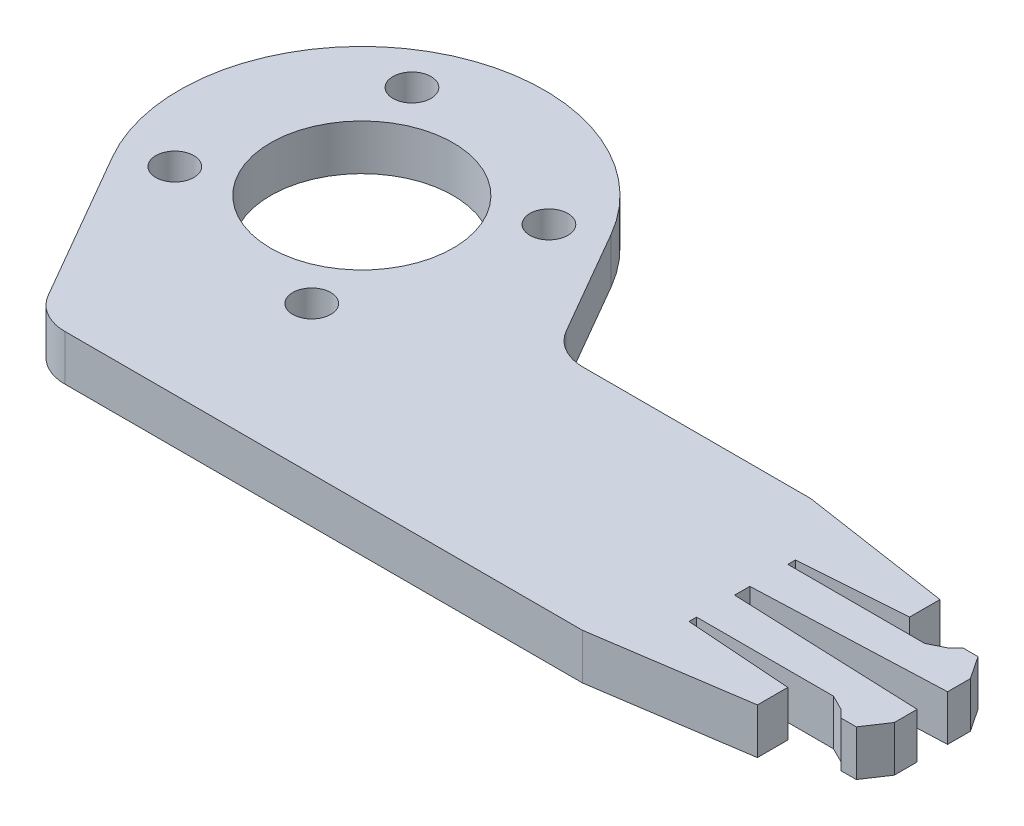
SolidWorks part; units mm, degrees
material "Lasercut ABS"
ref_plane "Front Plane" through (0, 0, 0) normal (0, 0, 1) x (1, 0, 0)
ref_plane "Top Plane" through (0, 0, 0) normal (0, 1, 0) x (1, 0, 0)
ref_plane "Right Plane" through (0, 0, 0) normal (1, 0, 0) x (0, 0, -1)
sketch "Sketch1" plane through (0, 0, 0) normal (0, 1, 0) x (1, 0, 0)
  line L0 (0, 0) -> (0, -10) construction
  line L1 (-4.5, 7.7942) -> (4.5, -7.7942) construction
  line L2 (-7.7942, -4.5) -> (7.7942, 4.5) construction
  line L3 (10.3923, 6) -> (15.2998, -2.5)
  line L4 (15.2998, -2.5) -> (32, -2.5)
  line L5 (-10.3923, -6) -> (-3.7528, -17.5)
  line L6 (-3.7528, -17.5) -> (32, -17.5)
  circle A0 centre (0, 0) radius 6
  circle A1 centre (0, 0) radius 9 construction
  circle A2 centre (7.7942, 4.5) radius 1.25
  circle A3 centre (-4.5, 7.7942) radius 1.25
  circle A4 centre (-7.7942, -4.5) radius 1.25
  circle A5 centre (4.5, -7.7942) radius 1.25
  arc A6 (10.3923, 6) -> (-10.3923, -6) centre (0, 0) ccw
  line B0 (32, -10) -> (35, -10) construction
  line B1 (35, -9.5) -> (35, -10.5)
  line B2 (35, -9.5) -> (47.5, -9)
  line B3 (47.5, -9) -> (47.5, -7.5)
  line B4 (47.5, -7.5) -> (46.5, -6)
  line B5 (46.5, -6) -> (45.5, -6)
  line B6 (45.5, -6) -> (45, -6.5)
  line B7 (45, -6.5) -> (44, -7)
  line B8 (44, -7) -> (35, -7)
  line B9 (35, -7) -> (35, -6.5)
  line B10 (35, -6.5) -> (42, -6)
  line B11 (42, -6) -> (42, -4)
  line B12 (42, -4) -> (32, -2.5)
  line B13 (35, -10.5) -> (47.5, -11)
  line B14 (47.5, -11) -> (47.5, -12.5)
  line B15 (47.5, -12.5) -> (46.5, -14)
  line B16 (46.5, -14) -> (45.5, -14)
  line B17 (45.5, -14) -> (45, -13.5)
  line B18 (45, -13.5) -> (44, -13)
  line B19 (44, -13) -> (35, -13)
  line B20 (35, -13) -> (35, -13.5)
  line B21 (35, -13.5) -> (42, -14)
  line B22 (42, -14) -> (42, -16)
  line B23 (42, -16) -> (32, -17.5)
  dimension "D1" = 12
  dimension "D5" = 18
  dimension "D6" = 2.5
  dimension "D7" = 24
  dimension "D2" = 10
  dimension "D3" = 42
  dimension "D4" = 30
sketch_block_instance "Block-Snap-Textile-1"
sketch_block "Block-Snap-Textile" parameters "D1"=3, "D2"=1, "D3"=2, "D4"=1.5, "D5"=10, "D6"=0.5, "D7"=9, "D8"=1, "D9"=0.5, "D10"=0.5, "D11"=0.5, "D12"=1, "D13"=12.5, "D14"=0.5, "D15"=0.5, "D16"=1.5, "D17"=1.5
extrude "Boss-Extrude1" add sketch "Sketch1" along normal mid plane 3 contours B23 B22 B21 B20 B19 B18 B17 B16 B15 B14 B13 B1 B2 B3 B4 B5 B6 B7 B8 B9 B10 B11 B12 L4 L3 A6 L5 L6 A5 A4 A3 A2 A0
fillet "Fillet1" radius 3 2 edges at (15.2998, 0, 2.5) (-3.7528, 0, 17.5)
sketch "Sketch2" plane through (0, 1.5, 0) normal (0, -1, 0) x (1, 0, 0)
  line L0 (28, 9) -> (12, 9) construction
  line L1 (28, 12.5) -> (12, 12.5) construction
  text T0 "M8" font "1CamBam_Stick_3" height 2.5
  text T1 "ONO V2" font "1CamBam_Stick_3" height 2.5
  dimension "D1" = 3.5
  dimension "D2" = 16
  dimension "D3" = 12
  dimension "D4" = 9
